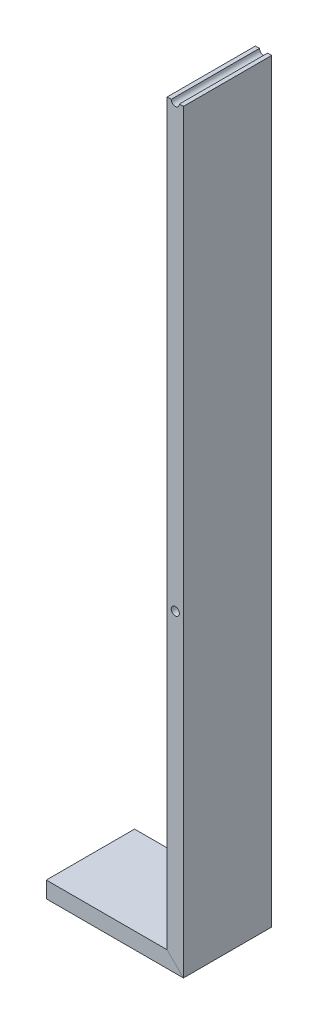
SolidWorks part; units mm, degrees
ref_plane "Płaszczyzna przednia" through (0, 0, 0) normal (0, 0, 1) x (1, 0, 0)
ref_plane "Płaszczyzna górna" through (0, 0, 0) normal (0, 1, 0) x (1, 0, 0)
ref_plane "Płaszczyzna prawa" through (0, 0, 0) normal (1, 0, 0) x (0, 0, -1)
sketch "Szkic1" plane through (0, 0, 0) normal (0, 0, 1) x (1, 0, 0)
  line L0 (0, 0) -> (190, 0)
  line L1 (190, 0) -> (190, 1100)
  dimension "D1" = 190
  dimension "D2" = 1100
ref_plane "Płaszczyzna1" through (0, 0, 0) normal (1, 0, 0) x (0, 0, -1)
sketch "Szkic2" plane through (0, 0, 0) normal (1, 0, 0) x (0, 0, -1)
  line L1 (65, -12) -> (-65, -12)
  line L2 (65, -12) -> (65, 12)
  line L3 (65, 12) -> (-65, 12)
  line L4 (-65, -12) -> (-65, 12)
  line L5 (65, -12) -> (-65, 12) construction
  line L6 (65, 12) -> (-65, -12) construction
  point P0 (0, 0)
  dimension "D1" = 130
  dimension "D2" = 24
sweep "Wyciągnięcie po ścieżce1" add profiles "Szkic2" path "Szkic1"
sketch "Szkic3" plane through (0, 0, 65) normal (0, 0, 1) x (1, 0, 0)
  line L0 (178, 1100) -> (202, 1100) construction
  line L1 (190, 1100) -> (190, 450) construction
  circle A0 centre (190, 1100) radius 6
  circle A1 centre (190, 450) radius 6
  dimension "D1" = 12
  dimension "D2" = 12
extrude "Wytnij-wyciągnięcie1" cut sketch "Szkic3" against normal through all
